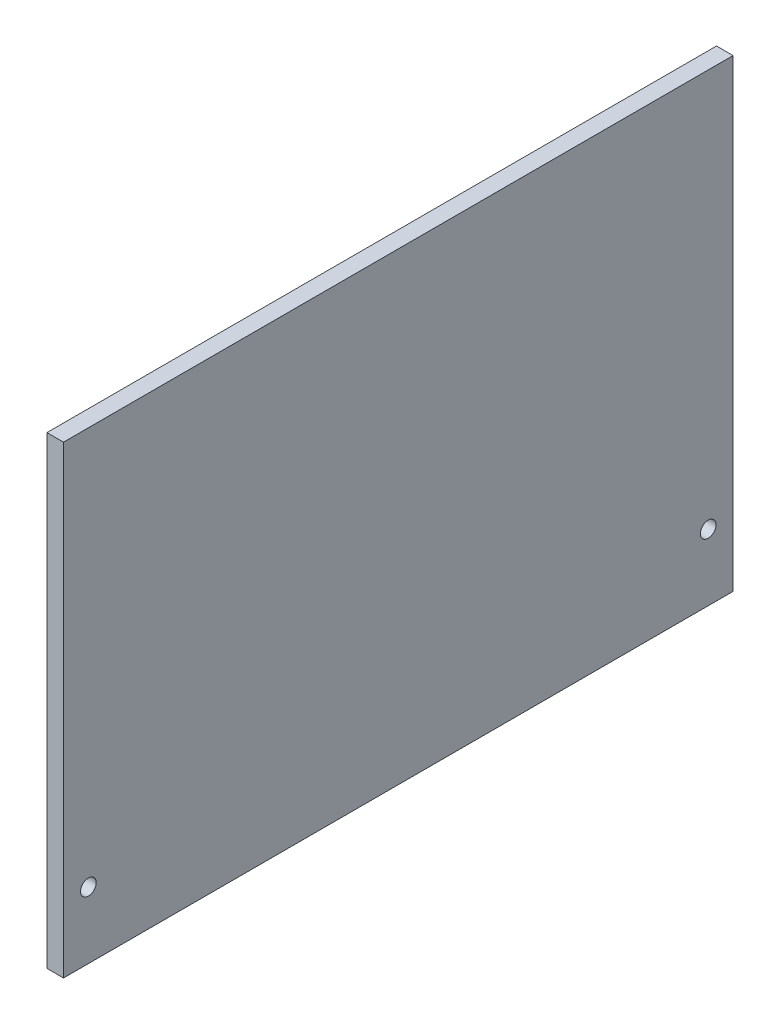
SolidWorks part; units mm, degrees
ref_plane "Front Plane" through (0, 0, 0) normal (0, 0, 1) x (1, 0, 0)
ref_plane "Top Plane" through (0, 0, 0) normal (0, 1, 0) x (1, 0, 0)
ref_plane "Right Plane" through (0, 0, 0) normal (1, 0, 0) x (0, 0, -1)
sketch "Sketch1" plane through (0, 0, 0) normal (1, 0, 0) x (0, 0, -1)
  line L0 (-59.3725, -31.75) -> (59.3725, -31.75) construction
  line L1 (64.135, 44.45) -> (-64.135, 44.45)
  line L2 (64.135, 44.45) -> (64.135, -44.45)
  line L3 (64.135, -44.45) -> (-64.135, -44.45)
  line L4 (-64.135, 44.45) -> (-64.135, -44.45)
  line L5 (64.135, 44.45) -> (-64.135, -44.45) construction
  line L6 (64.135, -44.45) -> (-64.135, 44.45) construction
  line L7 (0, -31.75) -> (0, 0) construction
  circle A0 centre (-59.3725, -31.75) radius 1.5
  circle A1 centre (59.3725, -31.75) radius 1.5
  point P0 (0, 0)
  dimension "D1" = 3
  dimension "D2" = 4.7625
  dimension "D3" = 128.27
  dimension "D4" = 12.7
  dimension "D5" = 76.2
extrude "Boss-Extrude1" add sketch "Sketch1" along normal blind 3.175
